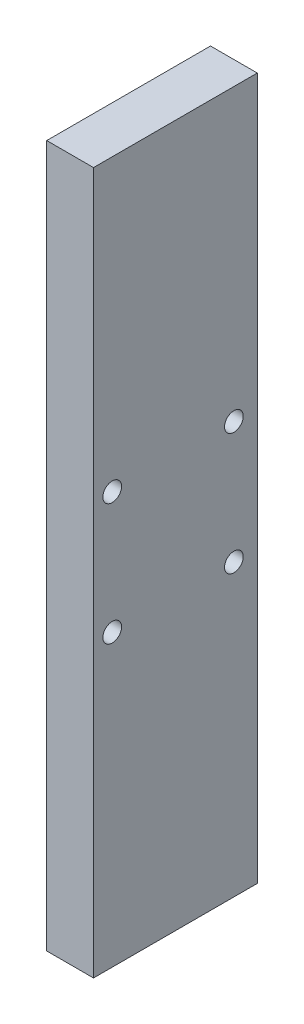
SolidWorks part; units mm, degrees
ref_plane "Front Plane" through (0, 0, 0) normal (0, 0, 1) x (1, 0, 0)
ref_plane "Top Plane" through (0, 0, 0) normal (0, 1, 0) x (1, 0, 0)
ref_plane "Right Plane" through (0, 0, 0) normal (1, 0, 0) x (0, 0, -1)
sketch "Sketch1" plane through (0, 0, 0) normal (1, 0, 0) x (0, 0, -1)
  line L1 (0, 0) -> (35, 0)
  line L2 (0, 0) -> (0, 150)
  line L3 (0, 150) -> (35, 150)
  line L4 (35, 0) -> (35, 150)
  dimension "D1" = 35
  dimension "D2" = 150
extrude "Boss-Extrude1" add sketch "Sketch1" along normal blind 10
sketch "Sketch2" plane through (10, 0, 0) normal (1, 0, 0) x (0, 0, -1)
  circle A4 centre (4, 88) radius 2
  circle A5 centre (30, 88) radius 2
  circle A6 centre (30, 62) radius 2
  circle A7 centre (4, 62) radius 2
  point P0 (0, 0)
  dimension "D3" = 4
  dimension "D1" = 26
  dimension "D2" = 26
extrude "Cut-Extrude1" cut sketch "Sketch2" against normal blind 10
